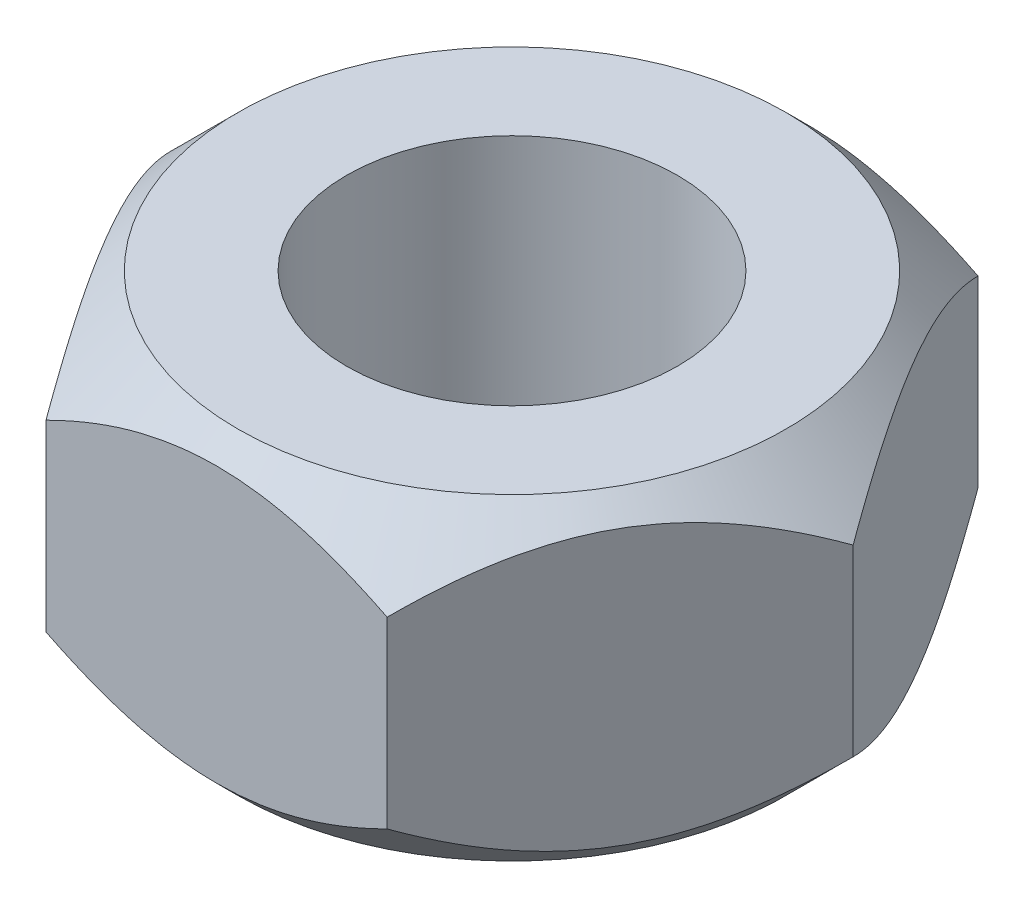
SolidWorks part; units mm, degrees
material "1023 Carbon Steel Sheet (SS)"
ref_plane "Front Plane" through (0, 0, 0) normal (0, 0, 1) x (1, 0, 0)
ref_plane "Top Plane" through (0, 0, 0) normal (0, 1, 0) x (1, 0, 0)
ref_plane "Right Plane" through (0, 0, 0) normal (1, 0, 0) x (0, 0, -1)
sketch "Sketch1" plane through (0, 0, 0) normal (0, 1, 0) x (1, 0, 0)
  line L0 (0, 0) -> (10.1086, 0) construction
  line L1 (-3.2079, 5.5563) -> (-6.4158, 0)
  line L2 (-6.4158, 0) -> (-3.2079, -5.5562)
  line L3 (-3.2079, -5.5562) -> (3.2079, -5.5562)
  line L4 (3.2079, -5.5562) -> (6.4158, 0)
  line L5 (6.4158, 0) -> (3.2079, 5.5563)
  line L6 (3.2079, 5.5563) -> (-3.2079, 5.5563)
  circle A0 centre (0, 0) radius 3.1115
  circle A1 centre (0, 0) radius 5.5562 construction
  dimension "D1" = 6.223
  dimension "D2" = 11.1125
extrude "Extrude1" add sketch "Sketch1" along normal mid plane 5.969
sketch "Sketch2" plane through (0, 2.9845, 0) normal (0, 1, 0) x (1, 0, 0)
  circle A0 centre (0, 0) radius 5.1562
  dimension "D1" = 10.3124
extrude "Extrude2" cut sketch "Sketch2" against normal blind 5.969 draft 45 flip side to cut
mirror "Mirror1" about plane through (0, 0, 0) normal (0, 1, 0) of "Extrude2"
